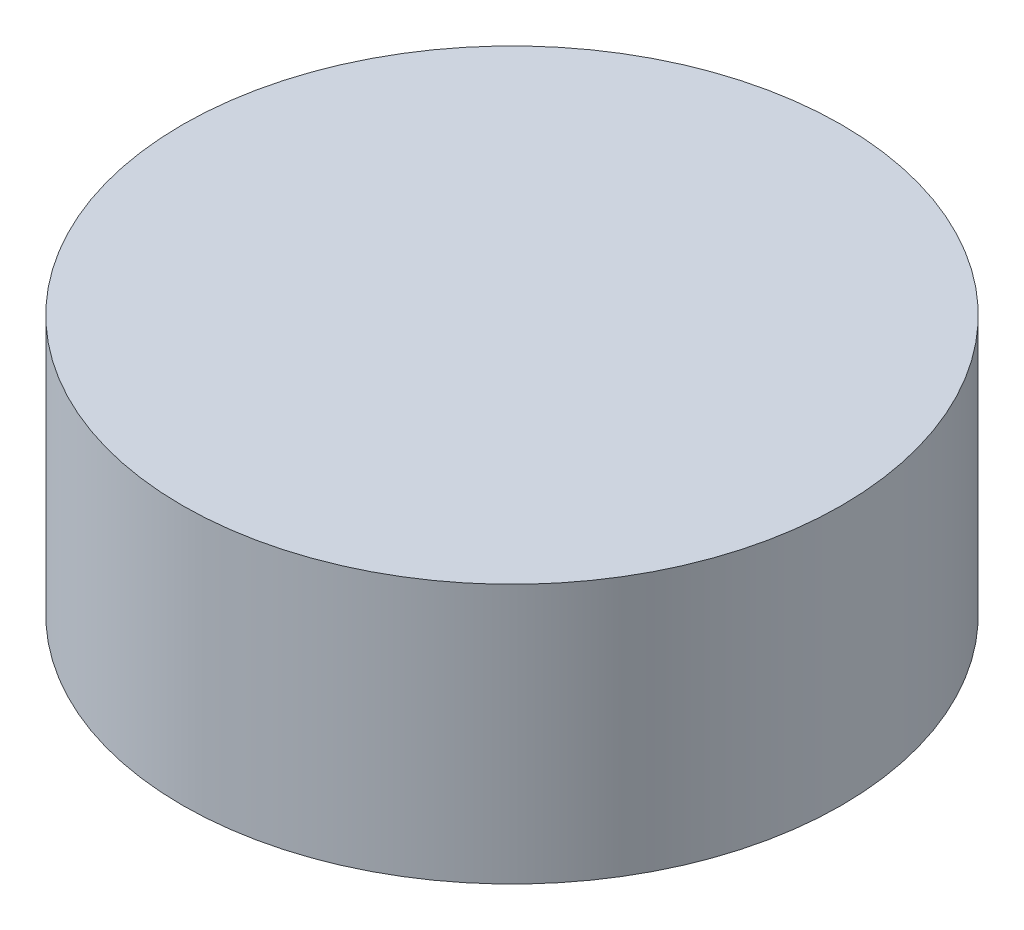
SolidWorks part; units mm, degrees
ref_plane "Front" through (0, 0, 0) normal (0, 0, 1) x (1, 0, 0)
ref_plane "Top" through (0, 0, 0) normal (0, 1, 0) x (1, 0, 0)
ref_plane "Right" through (0, 0, 0) normal (1, 0, 0) x (0, 0, -1)
sketch "ｽｹｯﾁ1" plane through (0, 0, 0) normal (0, 1, 0) x (1, 0, 0)
  circle A0 centre (0, 0) radius 25.4
  dimension "D1" = 50.8
extrude "ﾎﾞｽ - 押し出し1" add sketch "ｽｹｯﾁ1" along normal blind 20
